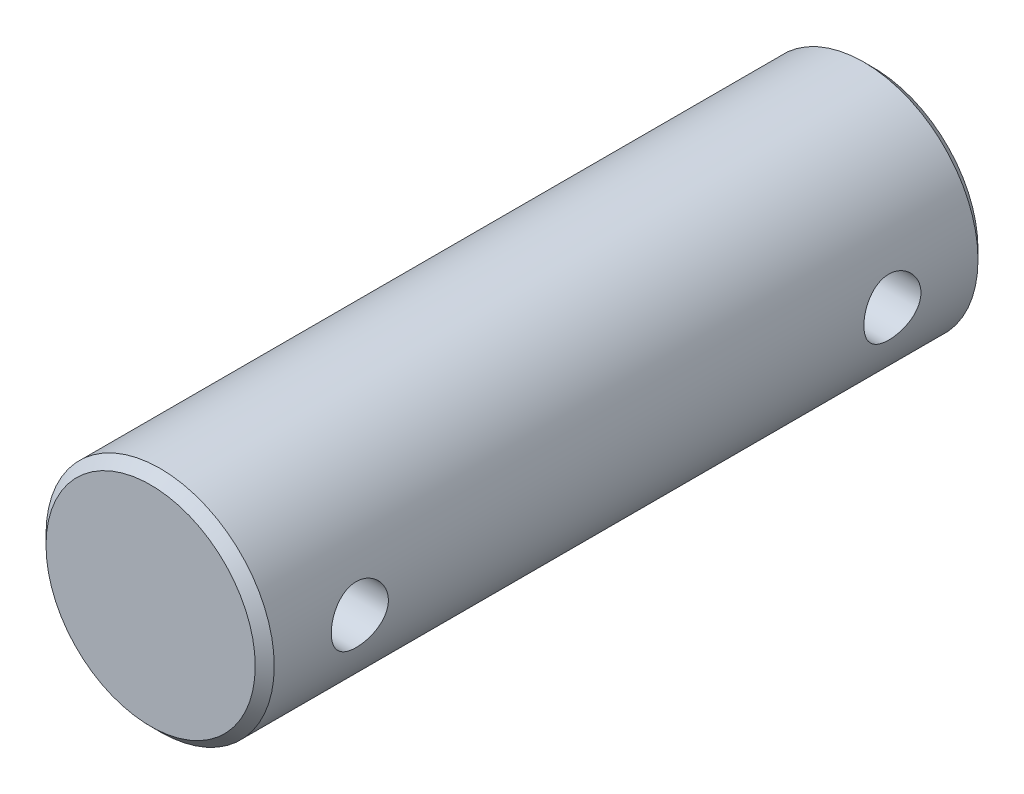
SolidWorks part; units mm, degrees
ref_plane "Front Plane" through (0, 0, 0) normal (0, 0, 1) x (1, 0, 0)
ref_plane "Top Plane" through (0, 0, 0) normal (0, 1, 0) x (1, 0, 0)
ref_plane "Right Plane" through (0, 0, 0) normal (1, 0, 0) x (0, 0, -1)
sketch "Sketch1" plane through (0, 0, 0) normal (0, 0, 1) x (1, 0, 0)
  circle A0 centre (0, 0) radius 6
  dimension "D1" = 12
extrude "Boss-Extrude1" add sketch "Sketch1" against normal blind 38
chamfer "Chamfer1" distance 0.5 angle 45 2 edges at (6, 0, -38) (6, 0, 0)
sketch "Sketch2" plane through (0, 0, 0) normal (1, 0, 0) x (0, 0, -1)
  line L0 (38, -5.5) -> (38, 5.5) construction
  circle A0 centre (5, 0) radius 1.5
  circle A1 centre (33, 0) radius 1.5
  point P7 (0, 0)
  dimension "D1" = 3
  dimension "D2" = 5
  dimension "D3" = 5
extrude "Cut-Extrude1" cut sketch "Sketch2" against normal through all both and the other way through all
